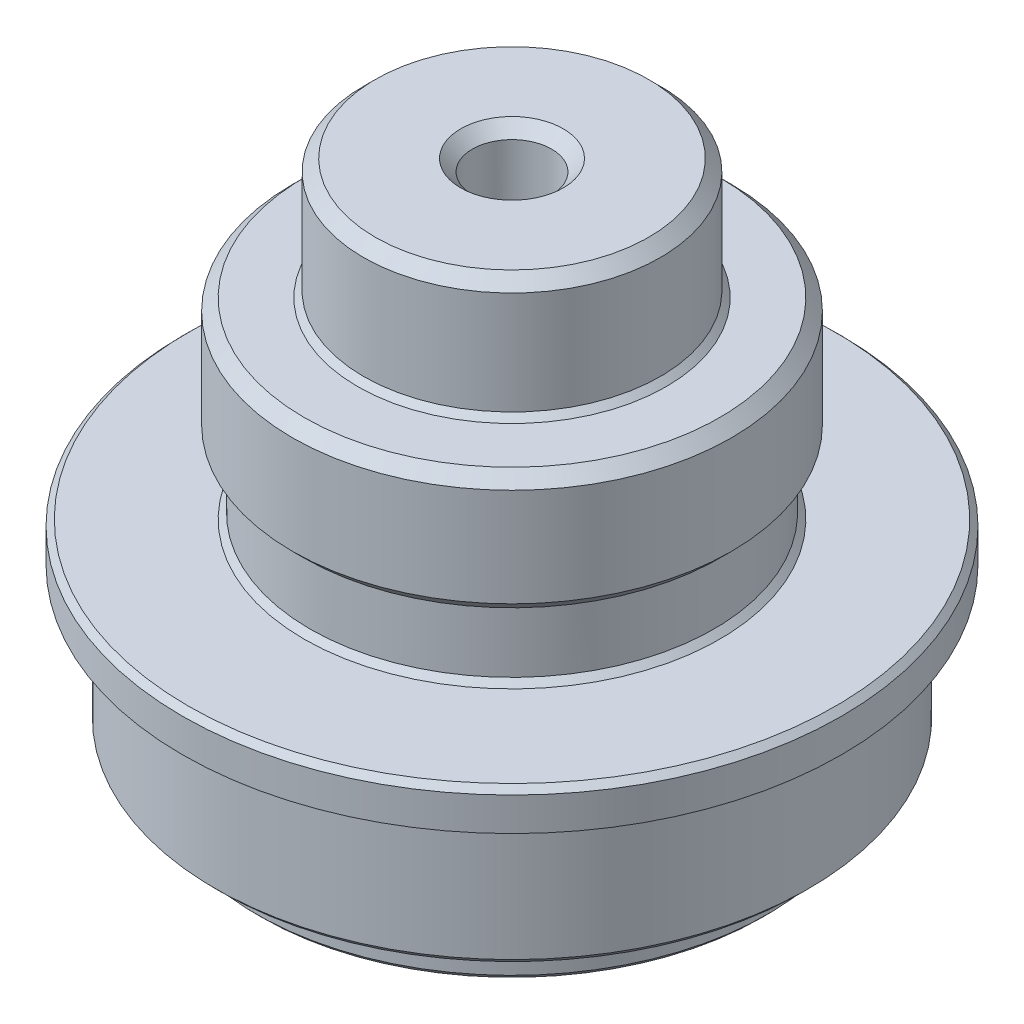
SolidWorks part; units mm, degrees
ref_plane "Front Plane" through (0, 0, 0) normal (0, 0, 1) x (1, 0, 0)
ref_plane "Top Plane" through (0, 0, 0) normal (0, 1, 0) x (1, 0, 0)
ref_plane "Right Plane" through (0, 0, 0) normal (1, 0, 0) x (0, 0, -1)
sketch "Sketch1" plane through (0, 0, 0) normal (0, 0, 1) x (1, 0, 0)
  line L0 (0, 0) -> (0, 45.5)
  line L1 (14.5286, 0) -> (21.8386, 0)
  line L2 (21.8386, 0) -> (21.8386, 3.65)
  line L3 (21.8386, 3.65) -> (25.35, 3.65)
  line L4 (25.35, 3.65) -> (25.35, 15.45)
  line L5 (25.35, 15.45) -> (28.1474, 15.45)
  line L6 (28.1474, 15.45) -> (28.1474, 18.8)
  line L7 (28.1474, 18.8) -> (17.25, 18.8)
  line L8 (17.25, 18.8) -> (17.25, 24.8)
  line L9 (17.25, 24.8) -> (18.75, 24.8)
  line L10 (18.75, 24.8) -> (18.75, 35.2)
  line L11 (18.75, 35.2) -> (12.68, 35.2)
  line L12 (12.68, 35.2) -> (12.68, 45.5)
  line L13 (12.68, 45.5) -> (3.38, 45.5)
  line L14 (14.5286, 0) -> (14.5286, 26.6296)
  line L15 (14.5286, 26.6296) -> (0, 26.6296)
  line L16 (12.68, 45.5) -> (3.38, 45.5)
  line L17 (3.38, 45.5) -> (3.38, 28)
  line L18 (3.38, 28) -> (0, 28)
  dimension "D1" = 45.5
  dimension "D2" = 12.68
  dimension "D3" = 7.31
  dimension "D4" = 3.65
  dimension "D5" = 11.8
  dimension "D6" = 3.35
  dimension "D7" = 6
  dimension "D8" = 10.4
  dimension "D9" = 18.75
  dimension "D10" = 1.5
  dimension "D11" = 9.3
  dimension "D12" = 17.5
  dimension "D13" = 25.35
revolve "Revolve1" add sketch "Sketch1" angle 360 about L0
chamfer "Chamfer2" distance 1 angle 45 3 edges at (0, 24.8, -18.75) (0, 35.2, -18.75) (0, 45.5, -3.38)
chamfer "Chamfer3" distance 1 angle 45 1 edges at (0, 45.5, -12.68)
chamfer "Chamfer4" distance 0.5 angle 45 6 edges at (0, 0, -14.5286) (0, 35.2, -12.68) (0, 18.8, -17.25) (0, 18.8, -28.1474) (0, 3.65, -25.35) (0, 0, -21.8386)
